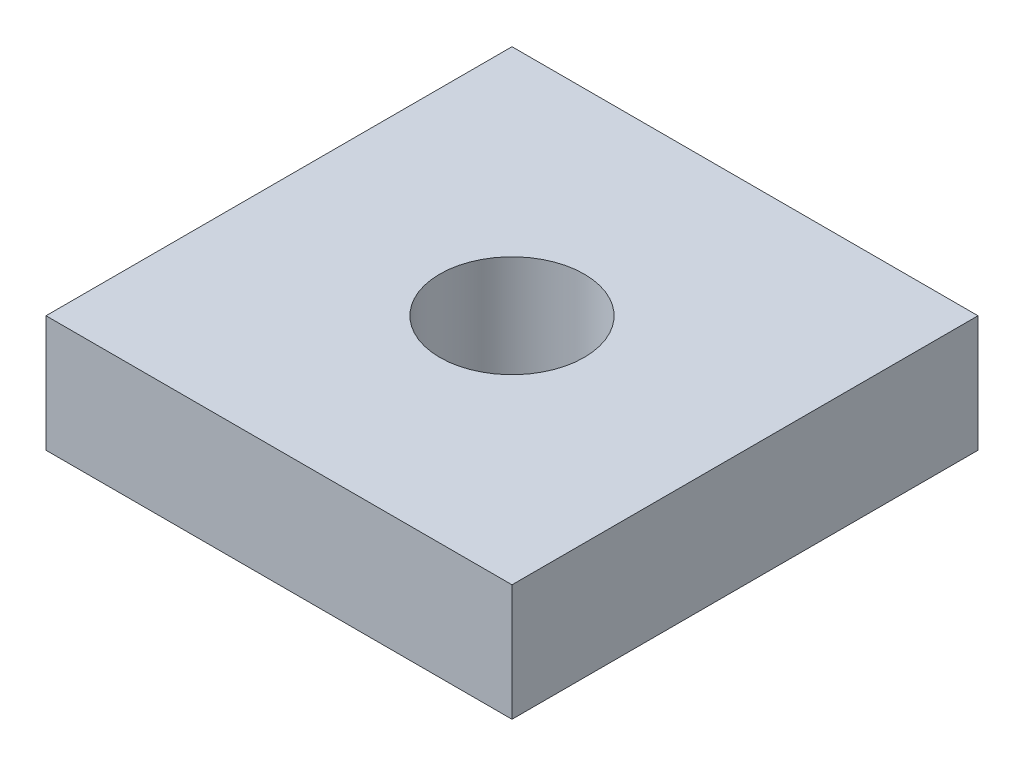
SolidWorks part; units mm, degrees
material "Maple"
ref_plane "Front Plane" through (0, 0, 0) normal (0, 0, 1) x (1, 0, 0)
ref_plane "Top Plane" through (0, 0, 0) normal (0, 1, 0) x (1, 0, 0)
ref_plane "Right Plane" through (0, 0, 0) normal (1, 0, 0) x (0, 0, -1)
sketch "Sketch1" plane through (0, 0, 0) normal (0, 1, 0) x (1, 0, 0)
  line L0 (0, 0) -> (50.8, 0)
  line L1 (0, 0) -> (0, 50.8)
  line L2 (50.8, 0) -> (50.8, 50.8)
  line L3 (0, 50.8) -> (50.8, 50.8)
  line L4 (0, 50.8) -> (50.8, 0) construction
  circle A0 centre (25.4, 25.4) radius 7.874
  dimension "D2" = 15.748
  dimension "D1" = 50.8
extrude "Boss-Extrude1" add sketch "Sketch1" along normal blind 12.7
